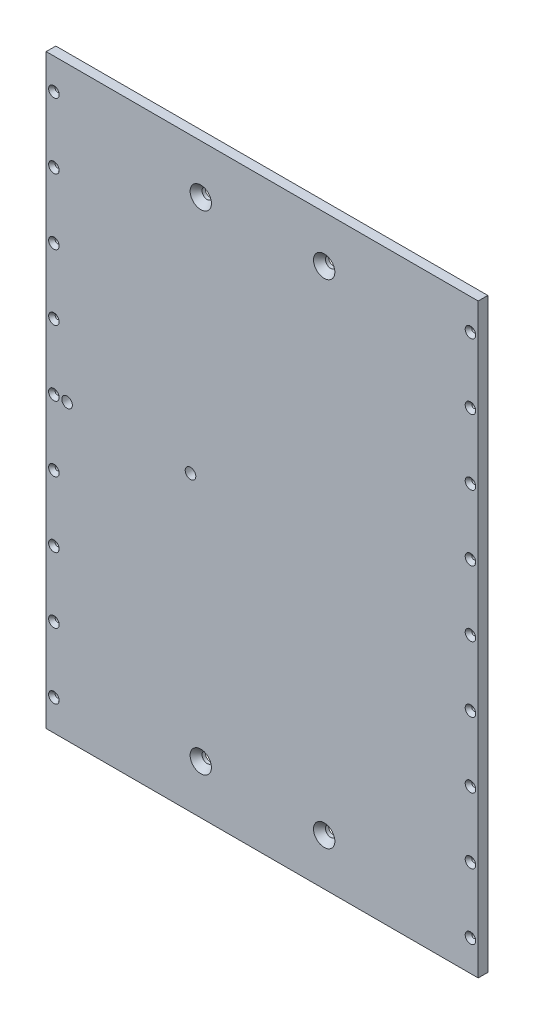
SolidWorks part; units mm, degrees
ref_plane "Front" through (0, 0, 0) normal (0, 0, 1) x (1, 0, 0)
ref_plane "Top" through (0, 0, 0) normal (0, 1, 0) x (1, 0, 0)
ref_plane "Right" through (0, 0, 0) normal (1, 0, 0) x (0, 0, -1)
sketch "Sketch1" plane through (0, 0, 0) normal (0, 0, 1) x (1, 0, 0)
  line L1 (-177.8, 241.3) -> (177.8, 241.3)
  line L2 (-177.8, 241.3) -> (-177.8, -241.3)
  line L3 (-177.8, -241.3) -> (177.8, -241.3)
  line L4 (177.8, 241.3) -> (177.8, -241.3)
  line L6 (0, 0) -> (0, 147.0663) construction
  dimension "D1" = 355.6
  dimension "D2" = 25.4
  dimension "D3" = 25.4
extrude "Extrude1" add sketch "Sketch1" along normal blind 7.9375
sketch "Sketch2" plane through (0, 0, 0) normal (0, 0, 1) x (1, 0, 0)
  line L0 (-71.3508, 241.3) -> (-71.3508, 213.4289)
  line L1 (177.8, 241.3) -> (-177.8, 241.3) construction
  line L2 (-71.3508, 213.4289) -> (71.3508, 213.4289)
  line L3 (71.3508, 213.4289) -> (71.3508, 241.3)
  line L4 (-71.3508, 241.3) -> (71.3508, 241.3)
  line L5 (-71.3508, -241.3) -> (-71.3508, -213.4289)
  line L7 (-177.8, -241.3) -> (177.8, -241.3) construction
  line L8 (-71.3508, -213.4289) -> (71.3508, -213.4289)
  line L9 (71.3508, -213.4289) -> (71.3508, -241.3)
  line L10 (71.3508, -241.3) -> (-71.3508, -241.3)
  dimension "D1" = 1.27
  dimension "D2" = 1.27
  dimension "D3" = 2.54
  dimension "D4" = 2.54
  dimension "D5" = 2.54
  dimension "D6" = 2.54
hole_wizard "5/16 Clearance Hole1" positions "Sketch11" profile "Sketch10" hole size "5/16" standard "Ansi Inch" end condition up to next
sketch "Sketch11" plane through (0, 0, 0) normal (0, 0, -1) x (-1, 0, 0)
  point P0 (59.0042, 0)
  point P1 (160.6042, 0)
  dimension "D1" = 101.6
sketch "Sketch10" plane through (-59.0042, 0, 0) normal (1, 0, 0) x (0, 1, 0)
  line L0 (0, 0) -> (0, 7.9375)
  line L1 (0, 7.9375) -> (4.365, 7.9375)
  line L2 (4.365, 7.9375) -> (4.365, 0)
  line L5 (4.365, 0) -> (0, 0)
  line L11 (0, -6.35) -> (0, 107.95) construction
  dimension "Thru Hole Dia." = 8.73
  dimension "Thru Hole Depth" = 7.9375
hole_wizard "CSK for 5/16 Flat Head Socket Cap Screw1" positions "Sketch13" profile "Sketch12" countersink size "5/16" standard "Ansi Inch" end condition up to next
sketch "Sketch13" plane through (0, 0, 7.9375) normal (0, 0, 1) x (1, 0, 0)
  point P0 (51.0361, 202.8187)
  point P1 (51.0361, -202.8187)
  point P2 (-50.5485, 201.0455)
  point P4 (-50.5485, -201.0455)
sketch "Sketch12" plane through (51.0361, 202.8187, 7.9375) normal (1, 0, 0) x (0, -1, 0)
  line L0 (0, 0) -> (0, 7.9375)
  line L1 (0, 7.9375) -> (4.2164, 7.9375)
  line L2 (4.2164, 7.9375) -> (4.2164, 5.2415)
  line L3 (4.2164, 5.2415) -> (8.7728, 0)
  line L5 (8.7728, 0) -> (0, 0)
  line L6 (-4.2164, 5.2415) -> (-8.7728, 0) construction
  line L11 (0, -6.35) -> (0, 107.95) construction
  dimension "Thru Hole Dia." = 8.4328
  dimension "Thru Hole Depth" = 7.9375
  dimension "Near C'Sink Dia." = 17.5456
  dimension "Near C'Sink Angle" = 82
hole_wizard "CSK for #6 Flat Head Socket Cap Screw1" positions "Sketch15" profile "Sketch14" countersink size "#6" standard "Ansi Inch"
sketch "Sketch15" plane through (0, 0, 7.9375) normal (0, 0, 1) x (1, 0, 0)
  line L0 (177.8, -241.3) -> (177.8, 241.3) construction
  line L1 (-177.8, 241.3) -> (-177.8, -241.3) construction
  line L2 (177.8, 0) -> (52.7849, 0) construction
  point P0 (-171.45, -215.9)
  point P1 (171.45, -215.9)
  point P6 (171.45, -161.925)
  point P8 (-171.45, -161.925)
  point P9 (171.45, -107.95)
  point P10 (-171.45, -107.95)
  point P11 (171.45, -53.975)
  point P12 (-171.45, -53.975)
  point P13 (171.45, 0)
  point P14 (-171.45, 0)
  point P15 (171.45, 53.975)
  point P16 (-171.45, 53.975)
  point P17 (171.45, 107.95)
  point P18 (-171.45, 107.95)
  point P19 (171.45, 161.925)
  point P20 (-171.45, 161.925)
  point P21 (171.45, 215.9)
  point P22 (-171.45, 215.9)
  dimension "D1" = 6.35
  dimension "D2" = 6.35
  dimension "D3" = 53.975
sketch "Sketch14" plane through (-171.45, -215.9, 7.9375) normal (1, 0, 0) x (0, -1, 0)
  line L0 (0, 0) -> (0, 9.0369)
  line L1 (0, 9.0369) -> (1.8288, 7.938)
  line L2 (1.8288, 7.938) -> (1.8288, 2.8894)
  line L3 (1.8288, 2.8894) -> (4.3405, 0)
  line L5 (4.3405, 0) -> (0, 0)
  line L6 (-1.8288, 2.8894) -> (-4.3405, 0) construction
  line L10 (0, 9.0369) -> (-1.8288, 7.938) construction
  line L11 (0, -6.35) -> (0, 107.95) construction
  dimension "Hole Dia." = 3.6576
  dimension "Hole Depth" = 7.938
  dimension "Near C'Sink Dia." = 8.681
  dimension "Near C'Sink Angle" = 82
  dimension "Drill Angle" = 118
